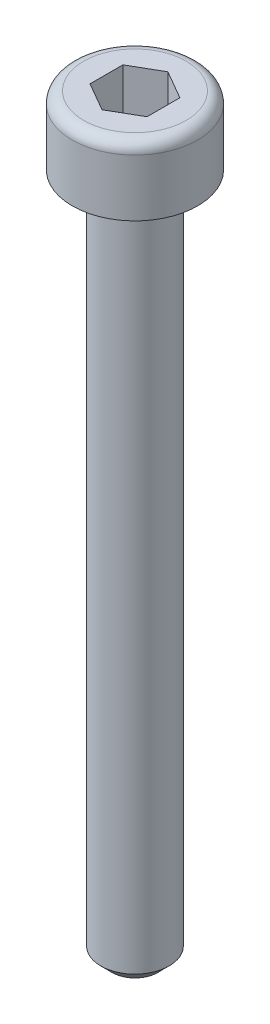
SolidWorks part; units mm, degrees
material "acero"
ref_plane "Alzado" through (0, 0, 0) normal (0, 0, 1) x (1, 0, 0)
ref_plane "Planta" through (0, 0, 0) normal (0, 1, 0) x (1, 0, 0)
ref_plane "Vista lateral" through (0, 0, 0) normal (1, 0, 0) x (0, 0, -1)
sketch "Croquis1" plane through (0, 0, 0) normal (0, 0, 1) x (1, 0, 0)
  line L0 (0, 0) -> (0, -60.9498) construction
  line L1 (0, 0) -> (2.75, 0)
  line L2 (2.75, 0) -> (2.75, -3)
  line L3 (2.75, -3) -> (1.5, -3)
  line L4 (1.5, -3) -> (1.5, -33)
  line L5 (1.5, -33) -> (0, -33)
  line L6 (0, -33) -> (0, 0)
  dimension "D1" = 30
  dimension "D2" = 3
  dimension "D3" = 5.5
  dimension "D4" = 3
revolve "Revolución1" add sketch "Croquis1" angle 360 about L0
sketch "Croquis2" plane through (0, 0, 0) normal (0, 1, 0) x (1, 0, 0)
  line L1 (1.25, 0.7217) -> (0, 1.4434)
  line L2 (0, 1.4434) -> (-1.25, 0.7217)
  line L3 (-1.25, 0.7217) -> (-1.25, -0.7217)
  line L4 (-1.25, -0.7217) -> (0, -1.4434)
  line L5 (0, -1.4434) -> (1.25, -0.7217)
  line L6 (1.25, -0.7217) -> (1.25, 0.7217)
  circle A0 centre (0, 0) radius 1.25 construction
  dimension "D1" = 2.5
extrude "Cortar-Extruir1" cut sketch "Croquis2" against normal blind 2
chamfer "Chaflán1" distance 0.5 angle 45 1 edges at (0, -33, 1.5)
fillet "Redondeo1" radius 0.5 1 edges at (0, 0, 2.75)
